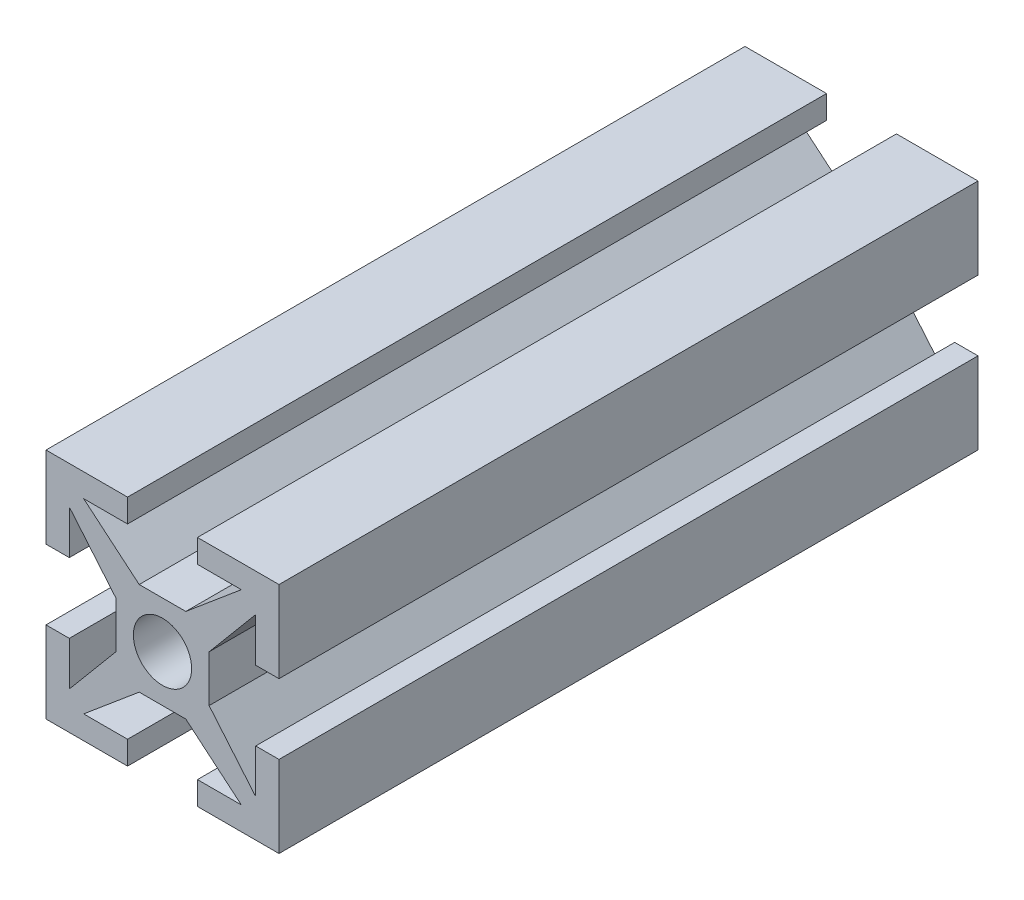
SolidWorks part; units mm, degrees
ref_plane "Front Plane" through (0, 0, 0) normal (0, 0, 1) x (1, 0, 0)
ref_plane "Top Plane" through (0, 0, 0) normal (0, 1, 0) x (1, 0, 0)
ref_plane "Right Plane" through (0, 0, 0) normal (1, 0, 0) x (0, 0, -1)
sketch "Esquisse2" plane through (0, 0, 0) normal (0, 0, 1) x (1, 0, 0)
  line L0 (-1, -2) -> (1, -2)
  line L1 (1, -2) -> (3.3835, -4)
  line L2 (3.3835, -4) -> (1.5, -4)
  line L3 (1.5, -4) -> (1.5, -5)
  line L4 (1.5, -5) -> (5, -5)
  line L5 (-1, -2) -> (-3.3835, -4)
  line L6 (-3.3835, -4) -> (-1.5, -4)
  line L7 (-1.5, -4) -> (-1.5, -5)
  line L8 (-1.5, -5) -> (-5, -5)
  line L9 (-5, -5) -> (-5, -1.5)
  line L10 (-5, -1.5) -> (-4, -1.5)
  line L11 (-4, -1.5) -> (-4, -3.3835)
  line L12 (-4, -3.3835) -> (-2, -1)
  line L13 (-2, -1) -> (-2, 1)
  line L14 (-2, 1) -> (-4, 3.3835)
  line L15 (-4, 3.3835) -> (-4, 1.5)
  line L16 (-4, 1.5) -> (-5, 1.5)
  line L17 (-5, 1.5) -> (-5, 5)
  line L18 (-5, 5) -> (-1.5, 5)
  line L19 (-1.5, 5) -> (-1.5, 4)
  line L20 (-1.5, 4) -> (-3.3835, 4)
  line L21 (-3.3835, 4) -> (-1, 2)
  line L22 (-1, 2) -> (1, 2)
  line L23 (1, 2) -> (3.3835, 4)
  line L24 (3.3835, 4) -> (1.5, 4)
  line L25 (1.5, 4) -> (1.5, 5)
  line L26 (1.5, 5) -> (5, 5)
  line L27 (5, 5) -> (5, 1.5)
  line L28 (5, 1.5) -> (4, 1.5)
  line L29 (4, 1.5) -> (4, 3.3835)
  line L30 (4, 3.3835) -> (2, 1)
  line L31 (2, -1) -> (2, 1)
  line L32 (2, -1) -> (4, -3.3835)
  line L33 (4, -3.3835) -> (4, -1.5)
  line L34 (4, -1.5) -> (5, -1.5)
  line L35 (5, -1.5) -> (5, -5)
  circle A0 centre (0, 0) radius 1.25
  point P4 (0, -2)
  point P34 (0, 2)
  point P40 (2, 0)
  dimension "D4" = 2.5
  dimension "D1" = 2
  dimension "D2" = 3.5
  dimension "D3" = 1
  dimension "D5" = 10
  dimension "D6" = 10
  dimension "D7" = 140
  dimension "D8" = 4
  dimension "D9" = 4
  dimension "D10" = 3.5
  dimension "D11" = 3
extrude "Main Extrusion" add sketch "Esquisse2" along normal blind 30
